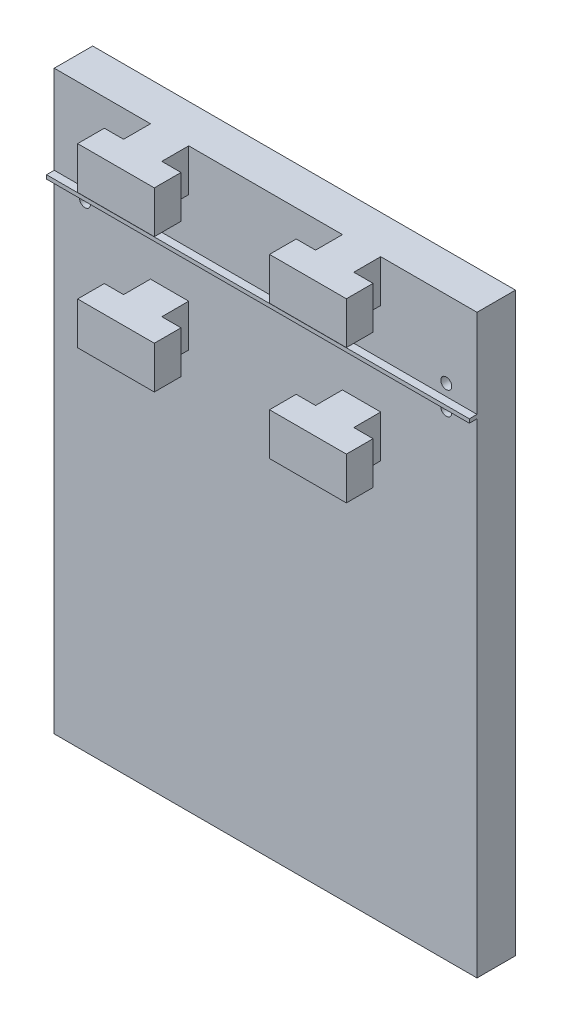
SolidWorks part; units mm, degrees
ref_plane "Front Plane" through (0, 0, 0) normal (0, 0, 1) x (1, 0, 0)
ref_plane "Top Plane" through (0, 0, 0) normal (0, 1, 0) x (1, 0, 0)
ref_plane "Right Plane" through (0, 0, 0) normal (1, 0, 0) x (0, 0, -1)
sketch "Sketch1" plane through (0, 0, 0) normal (0, 0, 1) x (1, 0, 0)
  line L1 (-93.2679, 5.384) -> (16.7321, 5.384)
  line L2 (-93.2679, 5.384) -> (-93.2679, -144.616)
  line L3 (-93.2679, -144.616) -> (16.7321, -144.616)
  line L4 (16.7321, 5.384) -> (16.7321, -144.616)
  dimension "D1" = 110
  dimension "D2" = 150
extrude "Boss-Extrude1" add sketch "Sketch1" along normal blind 10
sketch "Sketch2" plane through (0, 0, 10) normal (0, 0, 1) x (1, 0, 0)
  line L0 (-93.2679, 5.384) -> (-93.2679, -144.616) construction
  line L1 (-68.2279, 5.384) -> (-58.2779, 5.384)
  line L2 (-68.2279, 5.384) -> (-68.2279, -5.616)
  line L3 (-68.2279, -5.616) -> (-58.2779, -5.616)
  line L4 (-58.2779, 5.384) -> (-58.2779, -5.616)
  line L5 (-18.2779, 5.384) -> (-8.3279, 5.384)
  line L6 (-18.2779, 5.384) -> (-18.2779, -5.616)
  line L7 (-18.2779, -5.616) -> (-8.3279, -5.616)
  line L8 (-8.3279, 5.384) -> (-8.3279, -5.616)
  line L9 (16.7321, 5.384) -> (-93.2679, 5.384) construction
  dimension "D1" = 25.04
  dimension "D2" = 9.95
  dimension "D3" = 0
  dimension "D4" = 11
  dimension "D5" = 40
  dimension "D6" = 11
  dimension "D7" = 9.95
  dimension "D8" = 0
extrude "Boss-Extrude2" add sketch "Sketch2" along normal blind 7
sketch "Sketch3" plane through (0, 0, 17) normal (0, 0, 1) x (1, 0, 0)
  line L0 (-58.2779, 5.384) -> (-68.2279, 5.384) construction
  line L1 (-73.2279, 5.384) -> (-53.2779, 5.384)
  line L2 (-73.2279, 5.384) -> (-73.2279, -5.616)
  line L3 (-73.2279, -5.616) -> (-53.2779, -5.616)
  line L4 (-53.2779, 5.384) -> (-53.2779, -5.616)
  line L5 (-23.3079, 5.384) -> (-3.3079, 5.384)
  line L6 (-23.3079, 5.384) -> (-23.3079, -5.616)
  line L7 (-23.3079, -5.616) -> (-3.3079, -5.616)
  line L8 (-3.3079, 5.384) -> (-3.3079, -5.616)
  line L9 (-93.2679, 5.384) -> (-93.2679, -144.616) construction
  line L10 (-8.3279, 5.384) -> (-18.2779, 5.384) construction
  line L11 (16.7321, -144.616) -> (16.7321, 5.384) construction
  dimension "D1" = 0
  dimension "D2" = 11
  dimension "D3" = 20.04
  dimension "D4" = 19.95
  dimension "D5" = 0
  dimension "D6" = 11
  dimension "D7" = 20
  dimension "D8" = 20.04
extrude "Boss-Extrude3" add sketch "Sketch3" along normal blind 6.95
sketch "Sketch6" plane through (0, 0, 10) normal (0, 0, 1) x (1, 0, 0)
  line L0 (-93.2679, 5.384) -> (-93.2679, -144.616) construction
  line L1 (16.7321, -144.616) -> (16.7321, 5.384) construction
  line L2 (-68.2279, 5.384) -> (-93.2679, 5.384) construction
  line L3 (16.7321, 5.384) -> (-8.3279, 5.384) construction
  circle A0 centre (-85.2679, -20.616) radius 1.425
  circle A1 centre (8.7321, -20.616) radius 1.425
  dimension "D3" = 2.85
  dimension "D4" = 2.85
  dimension "D1" = 8
  dimension "D2" = 8
  dimension "D5" = 26
  dimension "D6" = 26
extrude "Cut-Extrude1" cut sketch "Sketch6" against normal blind 10
sketch "Sketch7" plane through (0, 0, 10) normal (0, 0, 1) x (1, 0, 0)
  line L0 (-93.2679, 5.384) -> (-93.2679, -144.616) construction
  line L1 (16.7321, -17.616) -> (-93.2679, -17.616)
  line L2 (16.7321, -17.616) -> (16.7321, -18.616)
  line L3 (16.7321, -18.616) -> (-93.2679, -18.616)
  line L4 (-93.2679, -17.616) -> (-93.2679, -18.616)
  line L5 (16.7321, -144.616) -> (16.7321, 5.384) construction
  line L6 (-68.2279, 5.384) -> (-93.2679, 5.384) construction
  dimension "D1" = 0
  dimension "D2" = 0
  dimension "D3" = 1
  dimension "D4" = 23
extrude "Boss-Extrude4" add sketch "Sketch7" along normal blind 2
mirror "Mirror1" about plane through (16.7321, -17.616, 12) normal (0, -1, 0) of "Cut-Extrude1", "Boss-Extrude2", "Boss-Extrude3"
